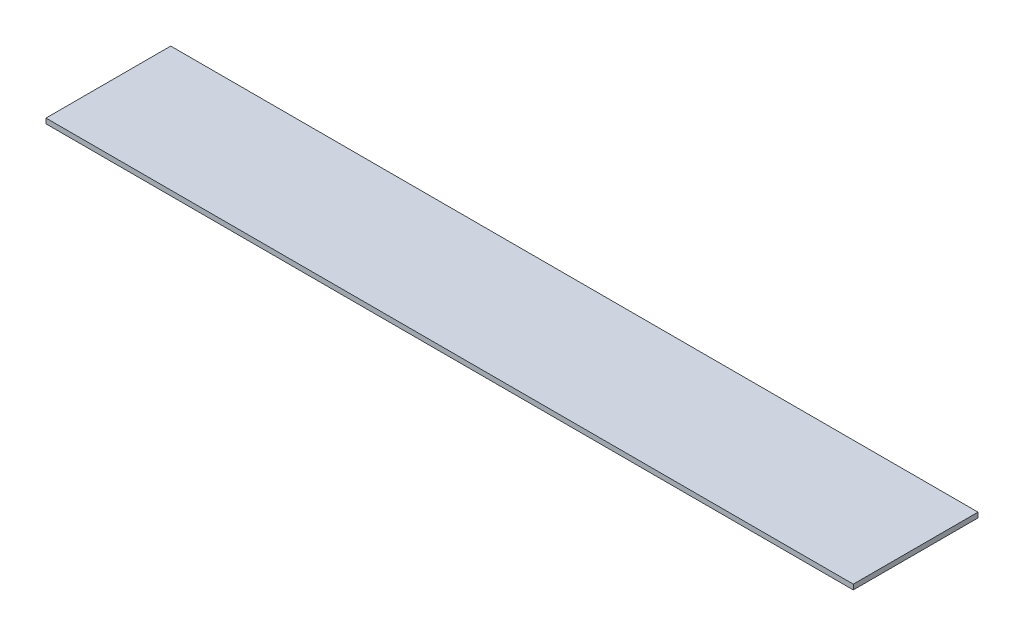
SolidWorks part; units mm, degrees
material "Custom Plastic"
ref_plane "Front Plane" through (0, 0, 0) normal (0, 0, 1) x (1, 0, 0)
ref_plane "Top Plane" through (0, 0, 0) normal (0, 1, 0) x (1, 0, 0)
ref_plane "Right Plane" through (0, 0, 0) normal (1, 0, 0) x (0, 0, -1)
sketch "Sketch1" plane through (0, 0, 0) normal (0, 1, 0) x (1, 0, 0)
  line L0 (0, 106.4209) -> (0, -50.5332)
  line L1 (0, -50.5332) -> (1016, -50.5332)
  line L2 (0, 106.4209) -> (1016, 106.4209)
  line L3 (1016, 106.4209) -> (1016, -50.5332)
extrude "Boss-Extrude1" add sketch "Sketch1" along normal blind 6.35 contours L1 L3 L2 L0
sketch "Sketch2" plane through (0, 6.35, 0) normal (0, 1, 0) x (1, 0, 0)
  line L0 (508, -50.5332) -> (508, -240.0298)
  line L1 (0, -50.5332) -> (1016, -50.5332) construction
